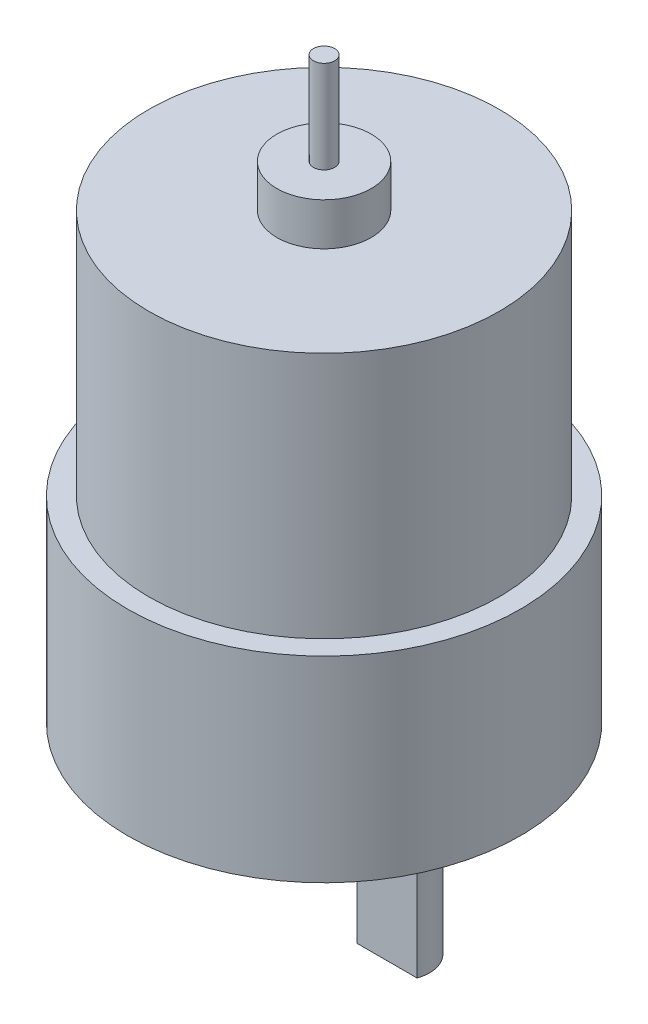
SolidWorks part; units mm, degrees
ref_plane "Piano frontale" through (0, 0, 0) normal (0, 0, 1) x (1, 0, 0)
ref_plane "Piano superiore" through (0, 0, 0) normal (0, 1, 0) x (1, 0, 0)
ref_plane "Piano destro" through (0, 0, 0) normal (1, 0, 0) x (0, 0, -1)
ref_plane "Piano1" through (0, 0, 0) normal (0, 0, -1) x (-1, 0, 0)
sketch "Schizzo1" plane through (0, 0, 0) normal (0, 0, -1) x (-1, 0, 0)
  line L0 (-18.5, -9.2456) -> (0, -9.2456)
  line L1 (0, -9.2456) -> (0, 9.2456)
  line L2 (0, 9.2456) -> (-18.5, 9.2456)
  line L3 (-18.5, 9.2456) -> (-18.5, -9.2456)
  line L4 (0, -9.2456) -> (0, 9.2456) construction
  dimension "D1" = 18.4912
  dimension "D2" = 18.5
revolve "Rivoluzione1" add sketch "Schizzo1" angle 360 about L4
sketch "Schizzo2" plane through (0, -9.2456, 0) normal (0, -1, 0) x (1, 0, 0)
  circle A0 centre (0, -6.95) radius 6
  circle A1 centre (0, 0) radius 18.5 construction
  dimension "D2" = 12
  dimension "D1" = 6.95
extrude "Estrusione-Estrusione1" add sketch "Schizzo2" along normal blind 4.572
sketch "Schizzo3" plane through (0, -13.8176, 0) normal (0, -1, 0) x (1, 0, 0)
  circle A0 centre (0, -6.95) radius 3
extrude "Estrusione-Estrusione2" add sketch "Schizzo3" along normal blind 17.83
sketch "Schizzo4" plane through (0, -31.6476, 0) normal (0, -1, 0) x (1, 0, 0)
  line L0 (-2.8217, -5.9311) -> (2.8217, -5.9311)
  arc A0 (2.8217, -5.9311) -> (-2.8217, -5.9311) centre (0, -6.95) ccw
extrude "Taglio-Estrusione1" cut sketch "Schizzo4" against normal blind 11.98
sketch "Schizzo5" plane through (0, 9.2456, 0) normal (0, 1, 0) x (-1, 0, 0)
  circle A0 centre (0, 0) radius 16.5
  dimension "D1" = 33
extrude "Estrusione-Estrusione3" add sketch "Schizzo5" along normal blind 23.2918
sketch "Schizzo6" plane through (0, 32.5374, 0) normal (0, 1, 0) x (-1, 0, 0)
  circle A0 centre (0, 0) radius 4.445
extrude "Estrusione-Estrusione4" add sketch "Schizzo6" along normal blind 4
sketch "Schizzo7" plane through (0, 36.5374, 0) normal (0, 1, 0) x (-1, 0, 0)
  circle A0 centre (0, 0) radius 1
extrude "Estrusione-Estrusione5" add sketch "Schizzo7" along normal blind 8.7
hole_wizard "Foro Ø3.0 (3)-1" positions "Schizzo9" profile "Schizzo8" hole size "Ø3.0" standard "Ansi Metric"
sketch "Schizzo9" plane through (0, -9.2456, 0) normal (0, -1, 0) x (-1, 0, 0)
  point P0 (15.5, 0)
  point P1 (7.75, -13.4234)
  point P2 (-15.5, 0)
  point P3 (7.75, 13.4234)
sketch "Schizzo8" plane through (-15.5, -9.2456, 0) normal (1, 0, 0) x (0, 0, -1)
  line L0 (0, 0) -> (0, 6)
  line L1 (0, 6) -> (1.5, 6)
  line L2 (1.5, 6) -> (1.5, 0)
  line L5 (1.5, 0) -> (0, 0)
  line L10 (0, 6) -> (-1.5, 6) construction
  line L11 (0, -6.35) -> (0, 107.95) construction
  dimension "Hole Dia." = 3
  dimension "Hole Depth" = 6
  dimension "Drill Angle" = 180
hole_wizard "Foro Ø3.0 (3)-2" positions "Schizzo11" profile "Schizzo10" hole size "Ø3.0" standard "Ansi Metric"
sketch "Schizzo11" plane through (0, -9.2456, 0) normal (0, -1, 0) x (-1, 0, 0)
  point P0 (13.8545, 6.95)
  point P1 (-13.8545, 6.95)
  point P2 (0, -15.5)
sketch "Schizzo10" plane through (-13.8545, -9.2456, -6.95) normal (1, 0, 0) x (0, 0, -1)
  line L0 (0, 0) -> (0, 10)
  line L1 (0, 10) -> (1.5, 10)
  line L2 (1.5, 10) -> (1.5, 0)
  line L5 (1.5, 0) -> (0, 0)
  line L10 (0, 10) -> (-1.5, 10) construction
  line L11 (0, -6.35) -> (0, 107.95) construction
  dimension "Hole Dia." = 3
  dimension "Hole Depth" = 10
  dimension "Drill Angle" = 180
equation "\"MaxDiameter\"= 3.7"
equation "\"D2@Schizzo1\"=\"MaxRadius\""
equation "\"MaxRadius\"= \"MaxDiameter\" / 2"
equation "\"Diameter\"=3.3"
equation "\"D1@Schizzo5\"=\"Diameter\""
